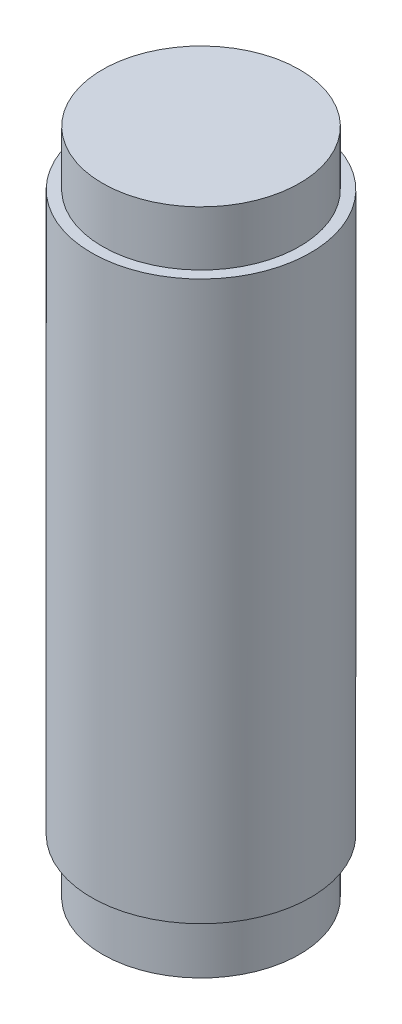
SolidWorks part; units mm, degrees
ref_plane "Front Plane" through (0, 0, 0) normal (0, 0, 1) x (1, 0, 0)
ref_plane "Top Plane" through (0, 0, 0) normal (0, 1, 0) x (1, 0, 0)
ref_plane "Right Plane" through (0, 0, 0) normal (1, 0, 0) x (0, 0, -1)
sketch "Sketch1" plane through (0, 0, 0) normal (0, 1, 0) x (1, 0, 0)
  circle A0 centre (0, 0) radius 5
extrude "Boss-Extrude1" add sketch "Sketch1" along normal blind 30.5
sketch "Sketch24" plane through (0, 0, 0) normal (0, -1, 0) x (-1, 0, 0)
  circle A0 centre (0, 0) radius 5
  circle A1 centre (0, 0) radius 4.5
  dimension "D1" = 0.5
extrude "Cut-Extrude3" cut sketch "Sketch24" against normal blind 2.5
sketch "Sketch25" plane through (0, 30.5, 0) normal (0, 1, 0) x (1, 0, 0)
  circle A0 centre (0, 0) radius 5
  circle A1 centre (0, 0) radius 4.5
  dimension "D1" = 0.5
extrude "Cut-Extrude4" cut sketch "Sketch25" against normal blind 2.5
